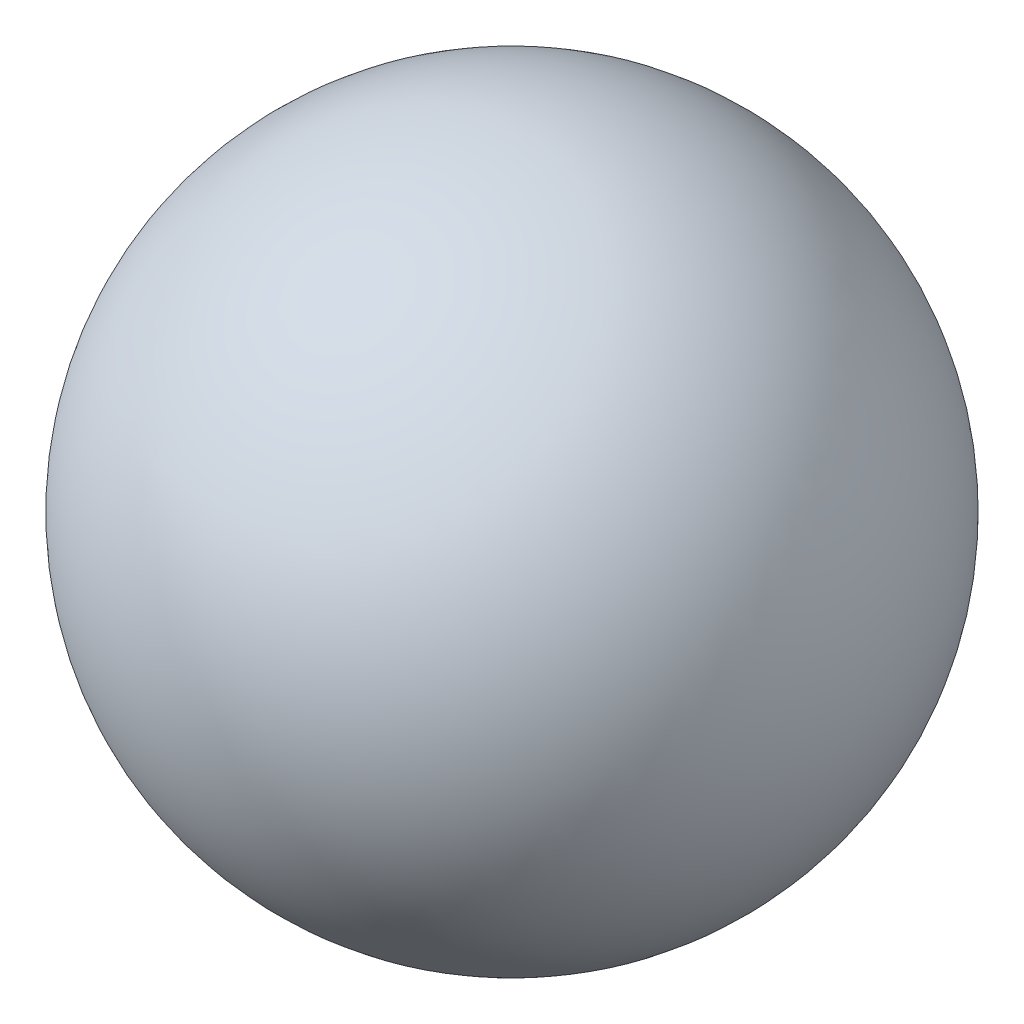
SolidWorks part; units mm, degrees
ref_plane "Front Plane" through (0, 0, 0) normal (0, 0, 1) x (1, 0, 0)
ref_plane "Top Plane" through (0, 0, 0) normal (0, 1, 0) x (1, 0, 0)
ref_plane "Right Plane" through (0, 0, 0) normal (1, 0, 0) x (0, 0, -1)
sketch "Sketch1" plane through (0, 0, 0) normal (0, 0, 1) x (1, 0, 0)
  line L0 (0, -0.5) -> (0, 0.5)
  arc A0 (0, 0.5) -> (0, -0.5) centre (0, 0) ccw
  dimension "D1" = 1
revolve "Revolve1" add sketch "Sketch1" angle 360 about L0
